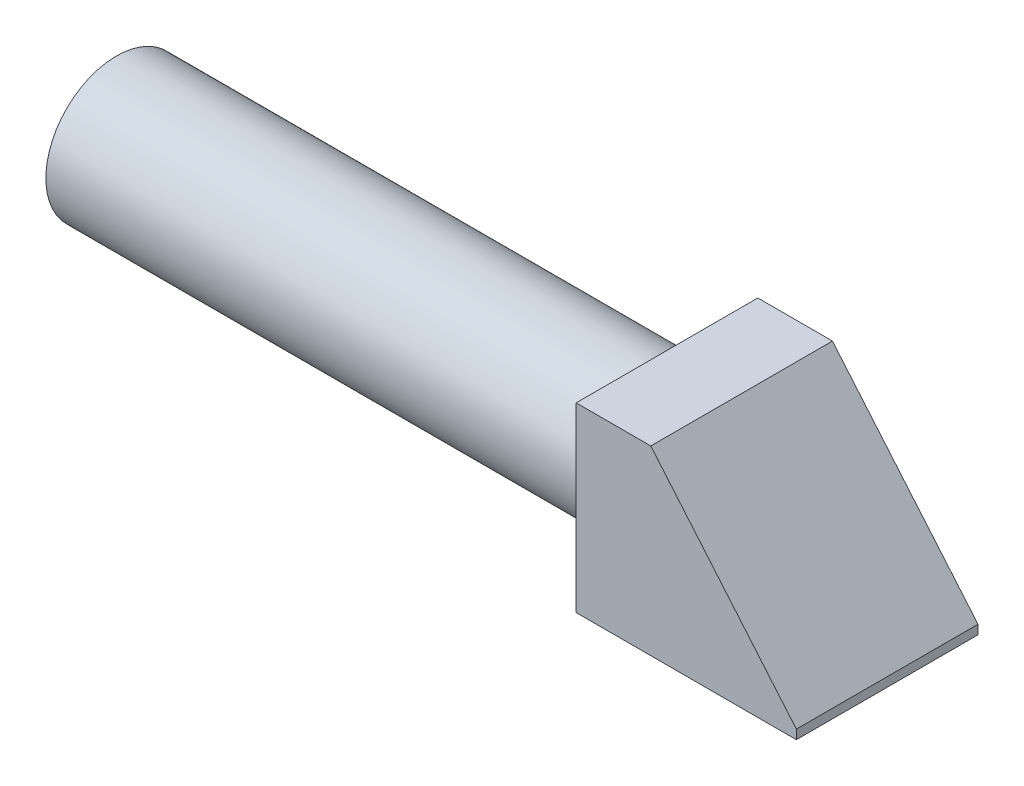
SolidWorks part; units mm, degrees
ref_plane "Front Plane" through (0, 0, 0) normal (0, 0, 1) x (1, 0, 0)
ref_plane "Top Plane" through (0, 0, 0) normal (0, 1, 0) x (1, 0, 0)
ref_plane "Right Plane" through (0, 0, 0) normal (1, 0, 0) x (0, 0, -1)
sketch "Sketch1" plane through (0, 0, 0) normal (1, 0, 0) x (0, 0, -1)
  circle A0 centre (0, 0) radius 3.85
  dimension "D1" = 7.7
extrude "Boss-Extrude1" add sketch "Sketch1" along normal blind 30
sketch "Sketch2" plane through (30, 0, 0) normal (1, 0, 0) x (0, 0, -1)
  circle A0 centre (0, 0) radius 3.25
  circle A1 centre (0, 0) radius 3.85
  circle A2 centre (0, 0) radius 3.85
  dimension "D2" = 6.5
  dimension "D1" = 0
extrude "Cut-Extrude1" cut sketch "Sketch2" against normal blind 1
sketch "Sketch3" plane through (30, 0, 0) normal (1, 0, 0) x (0, 0, -1)
  line L1 (-4.95, -4.95) -> (4.95, -4.95)
  line L2 (-4.95, -4.95) -> (-4.95, 4.95)
  line L3 (-4.95, 4.95) -> (4.95, 4.95)
  line L4 (4.95, -4.95) -> (4.95, 4.95)
  line L5 (-4.95, -4.95) -> (4.95, 4.95) construction
  line L6 (-4.95, 4.95) -> (4.95, -4.95) construction
  point P0 (0, 0)
  dimension "D1" = 9.9
extrude "Boss-Extrude2" add sketch "Sketch3" along normal blind 12
sketch "Sketch4" plane through (0, 0, 4.95) normal (0, 0, 1) x (1, 0, 0)
  line L0 (34.0672, 4.95) -> (42, -4.45)
  line L1 (42, 4.95) -> (30, 4.95) construction
  line L2 (42, 4.95) -> (42, -4.95) construction
  line L3 (34.0672, 4.95) -> (42, 4.95)
  line L4 (42, 4.95) -> (42, -4.45)
  dimension "D1" = 0.5
  dimension "D2" = 12.3
extrude "Cut-Extrude2" cut sketch "Sketch4" against normal blind 12
